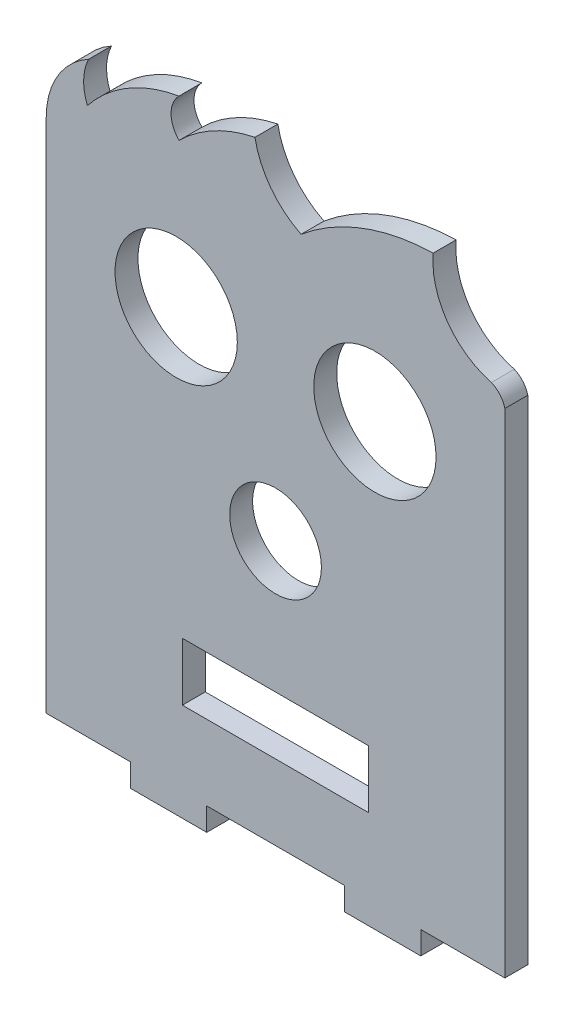
SolidWorks part; units mm, degrees
ref_plane "Alzado" through (0, 0, 0) normal (0, 0, 1) x (1, 0, 0)
ref_plane "Planta" through (0, 0, 0) normal (0, 1, 0) x (1, 0, 0)
ref_plane "Vista lateral" through (0, 0, 0) normal (1, 0, 0) x (0, 0, -1)
sketch "Model" plane through (0, 0, 0) normal (0, 0, 1) x (1, 0, 0)
  line L0 (11, -3) -> (21, -3)
  line L1 (0, 33.2625) -> (0, 11.5201)
  line L2 (0, 57.3746) -> (0, 33.2625)
  line L3 (0, 11.5201) -> (0, 0)
  line L4 (0, 0) -> (11, 0)
  line L5 (11, 0) -> (11, -3)
  line L6 (21, -3) -> (21, 0)
  line L7 (21, 0) -> (39, 0)
  line L8 (39, 0) -> (39, -3)
  line L9 (0, 67.5251) -> (0, 57.3746)
  line L10 (60, 0) -> (60, 64.5251)
  line L11 (49, 0) -> (60, 0)
  line L12 (49, -3) -> (49, 0)
  line L13 (17.81, 17.3991) -> (17.81, 9.8191)
  line L14 (17.81, 9.8191) -> (42.19, 9.8191)
  line L15 (42.19, 9.8191) -> (42.19, 17.3991)
  line L16 (42.19, 17.3991) -> (17.81, 17.3991)
  line L17 (49, -3) -> (39, -3)
  circle A0 centre (43, 54.5251) radius 8
  circle A1 centre (17, 54.5251) radius 8
  circle A2 centre (30, 34.5251) radius 6
  arc A3 (60, 64.5251) -> (58.2416, 66.5923) centre (57.0828, 63.8251) ccw
  arc A4 (50.6228, 77.443) -> (58.2416, 66.5923) centre (60.8921, 76.5534) ccw
  arc A5 (50.6228, 77.443) -> (33.3422, 70.9352) centre (51.2729, 49.5196) ccw
  arc A6 (27.3054, 78.9074) -> (33.3422, 70.9352) centre (38.296, 80.9581) ccw
  arc A7 (27.3054, 78.9074) -> (17.3798, 73.5975) centre (31.2979, 59.5128) ccw
  arc A8 (17.3568, 78.5975) -> (17.3798, 73.5975) centre (19.8683, 76.109) ccw
  arc A9 (17.3568, 78.5975) -> (5.3892, 71.5422) centre (20.5448, 59.512) ccw
  arc A10 (5.5362, 76.8649) -> (5.3892, 71.5422) centre (11.4112, 74.0393) ccw
  arc A11 (5.5362, 76.8649) -> (0, 67.5251) centre (10.6447, 67.5262) ccw
extrude "Saliente-Extruir1" add sketch "Model" along normal blind 3
